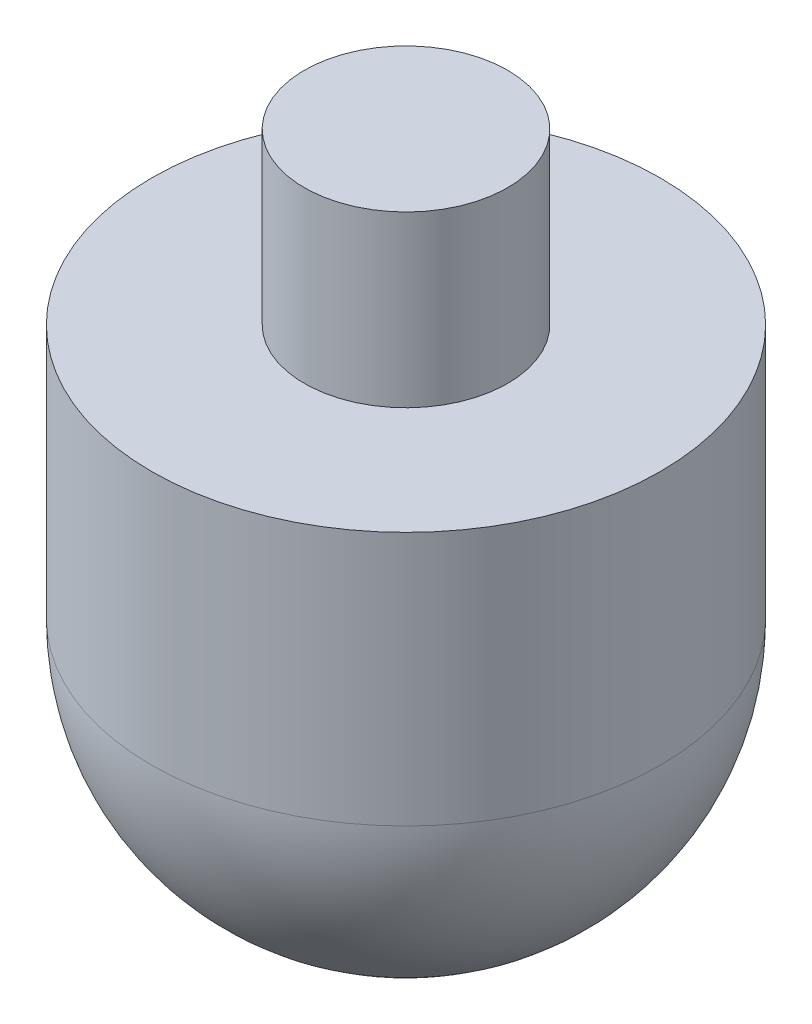
SolidWorks part; units mm, degrees
ref_plane "Front Plane" through (0, 0, 0) normal (0, 0, 1) x (1, 0, 0)
ref_plane "Top Plane" through (0, 0, 0) normal (0, 1, 0) x (1, 0, 0)
ref_plane "Right Plane" through (0, 0, 0) normal (1, 0, 0) x (0, 0, -1)
sketch "Sketch1" plane through (0, 0, 0) normal (0, 0, 1) x (1, 0, 0)
  line L0 (0, 0) -> (0, 68.9722) construction
  line L1 (15, 0) -> (15, 15)
  line L2 (15, 15) -> (6, 15)
  line L3 (6, 15) -> (6, 25)
  line L4 (6, 25) -> (0, 25)
  line L5 (0, 25) -> (0, -15)
  arc A0 (15, 0) -> (0, -15) centre (0, 0) cw
  dimension "D1" = 25
  dimension "D2" = 10
  dimension "D3" = 12
  dimension "D4" = 30
revolve "Revolve1" add sketch "Sketch1" angle 360 about L0
